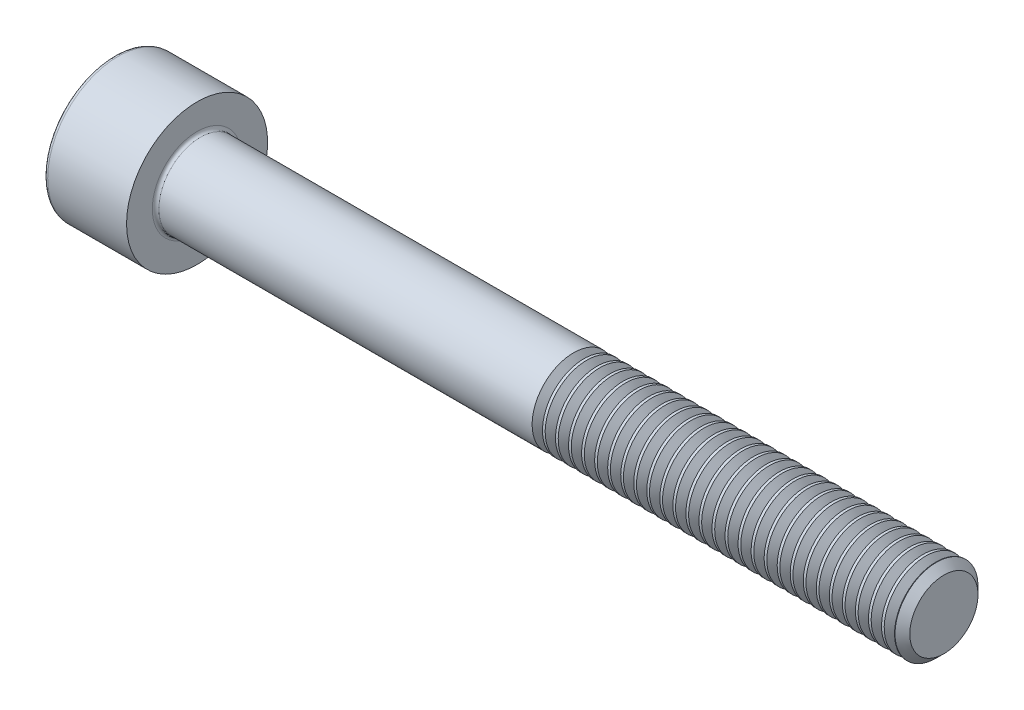
SolidWorks part; units mm, degrees
revolve "Base-Revolve" add sketch "BodySke"
sketch "BodySke" plane through (0, 0, 0) normal (0, 0, 1) x (1, 0, 0)
  line L0 (0, 0) -> (0, 4.25)
  line L1 (0, 4.25) -> (5, 4.25)
  line L2 (5, 4.25) -> (5, 2.5)
  line L3 (5, 2.5) -> (49.555, 2.5)
  line L4 (50, 2.055) -> (50, 0)
  line L5 (50, 0) -> (0, 0)
  line L6 (-31.75, 0) -> (127, 0) construction
  line L8 (50, 2.055) -> (49.555, 2.5)
  line L10 (50, -2.055) -> (49.555, -2.5) construction
  line L11 (5.8, 9.525) -> (5.8, 3.175) construction
  line L12 (28, 9.525) -> (28, 3.175) construction
  line L13 (-10, 9.525) -> (-10, 3.175) construction
  dimension "Head_ht" = 5
  dimension "Length" = 45
  dimension "Body_ch_ang" = 45
  dimension "Diameter" = 5
  dimension "Minor_dia" = 4.11
  dimension "Advance" = 0.8
  dimension "Thread_nom" = 22
  dimension "Thread_length" = 60
  dimension "Head_dia" = 8.5
cosmetic thread "ThreadCosmetic" [suppressed]
fillet "Fillet1" radius 0.2 1 edges at (5, 0, 2.5)
fillet "Fillet2" radius 0.25 1 edges at (0, 0, 4.25)
ref_plane "Plane1" through (0, 0, 0) normal (0, 0, 1) x (1, 0, 0)
ref_plane "Plane2" through (0, 0, 0) normal (0, 1, 0) x (1, 0, 0)
ref_plane "Plane3" through (0, 0, 0) normal (1, 0, 0) x (0, 0, -1)
sketch "Sketch2" plane through (0, 0, 0) normal (0, 0, 1) x (1, 0, 0)
  line L0 (0, 2.042) -> (2.5, 2.042)
  line L1 (2.5, 2.042) -> (3.6789, 0)
  line L2 (-31.75, 0) -> (127, 0) construction
  line L3 (3.6789, 0) -> (0, 0)
  line L4 (0, 0) -> (0, 2.042)
  line L6 (0, 0) -> (47.625, 0) construction
  dimension "D1" = 2.042
  dimension "D2" = 60
  dimension "Depth" = 2.5
revolve "Hex-PreBroach" cut sketch "Sketch2" angle 360 about L6
sketch "Sketch3" plane through (0, 0, 0) normal (-1, 0, 0) x (0, 0.5, 0.866)
  line L0 (1.1789, 2.042) -> (-1.1789, 2.042)
  line L1 (-1.1789, 2.042) -> (-2.3579, 0)
  line L2 (1.1789, 2.042) -> (2.3579, 0)
  line L3 (1.1789, -2.042) -> (2.3579, 0)
  line L4 (1.1789, -2.042) -> (-1.1789, -2.042)
  line L5 (-1.1789, -2.042) -> (-2.3579, 0)
  dimension "D1" = 2.042
  dimension "D2" = 2.042
  dimension "Hex_size" = 4.084
extrude "Hex" cut sketch "Sketch3" against normal blind 2.5
sketch "ThdSchSke" plane through (0, 0, 0) normal (0, 0, 1) x (1, 0, 0)
  line L0 (28, -2.055) -> (27.6884, -2.5)
  line L1 (28, -2.055) -> (28.3116, -2.5)
  line L2 (28.3116, -2.5) -> (28.3116, -3.125)
  line L3 (-3.175, 0) -> (5.1513, 0) construction
  line L4 (0, 4) -> (0, -4) construction
  line L5 (28.3116, -3.125) -> (27.6884, -3.125)
  line L6 (27.6884, -3.125) -> (27.6884, -2.5)
  dimension "Thread_minor" = 4.11
  dimension "Diameter" = 5
  dimension "Start" = 28
revolve "ThreadSchematic" cut sketch "ThdSchSke" angle 360 about L3
pattern_linear "ThdSchPat" count 28 spacing 0.7857 along (1, 0, 0) of "ThreadSchematic"
equation "\"D2@Sketch3\" = \"Hex_size@Sketch3\" / 2"
equation "\"D1@Sketch3\" = \"Hex_size@Sketch3\" / 2"
equation "\"D1@Sketch2\" = \"Hex_size@Sketch3\" / 2"
equation "\"Thread_minor@ThreadCosmetic\"  =  \"Minor_dia@BodySke\""
equation "\"Depth@Sketch2\" =  \"Key_eng@Hex\""
equation "\"Thread_length@ThreadCosmetic\" = ((sgn( (\"Length@BodySke\" - \"Advance@BodySke\" * 3.0) - \"Thread_nom@BodySke\" )-1)*( (\"Length@BodySke\" - \"Advance@BodySke\" * 3.0) - \"Thread_nom@BodySke\" ))/-2+ \"Thread_nom@BodySke\""
equation "\"Thread_minor@ThdSchSke\" = \"Minor_dia@BodySke\""
equation "\"Diameter@ThdSchSke\" = \"Diameter@BodySke\""
equation "\"Overcut@ThdSchSke\" = \"Diameter@BodySke\" * 1.25"
equation "\"Start@ThdSchSke\" = \"Head_ht@BodySke\" + \"Length@BodySke\" - \"Thread_length@ThreadCosmetic\"  '---Non-countersunk---"
equation "\"Num_threads@ThdSchPat\" = int( \"Thread_length@ThreadCosmetic\" / \"Advance@BodySke\" + 0.999 )  + 1"
equation "\"Advance@ThdSchPat\" = \"Thread_length@ThreadCosmetic\" /  (\"Num_threads@ThdSchPat\" - 1) 'relax it"
equation "\"Num_threads@ThdSchPat\" = \"Num_threads@ThdSchPat\" - sgn( \"Num_threads@ThdSchPat\" - 1) '---chamfered tips only---"
